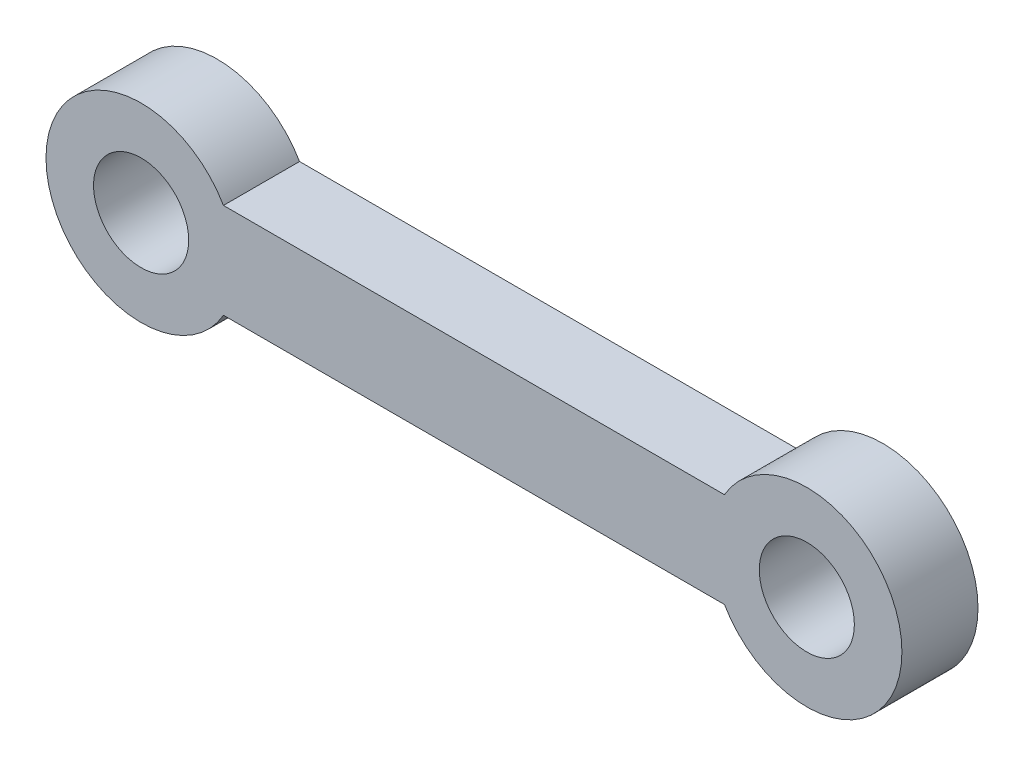
SolidWorks part; units mm, degrees
ref_plane "Front Plane" through (0, 0, 0) normal (0, 0, 1) x (1, 0, 0)
ref_plane "Top Plane" through (0, 0, 0) normal (0, 1, 0) x (1, 0, 0)
ref_plane "Right Plane" through (0, 0, 0) normal (1, 0, 0) x (0, 0, -1)
sketch "Sketch1" plane through (0, 0, 0) normal (0, 0, 1) x (1, 0, 0)
  line L0 (0, 0) -> (35, 0) construction
  line L1 (4.3301, 2.5) -> (30.6699, 2.5)
  line L2 (4.3301, -2.5) -> (30.6699, -2.5)
  circle A0 centre (0, 0) radius 5
  circle A1 centre (35, 0) radius 5
  circle A2 centre (0, 0) radius 2.5
  circle A3 centre (35, 0) radius 2.5
  dimension "D1" = 10
  dimension "D2" = 2.5
  dimension "D5" = 5
  dimension "D6" = 5
  dimension "D3" = 5
  dimension "D4" = 35
extrude "Boss-Extrude1" add sketch "Sketch1" along normal blind 4
